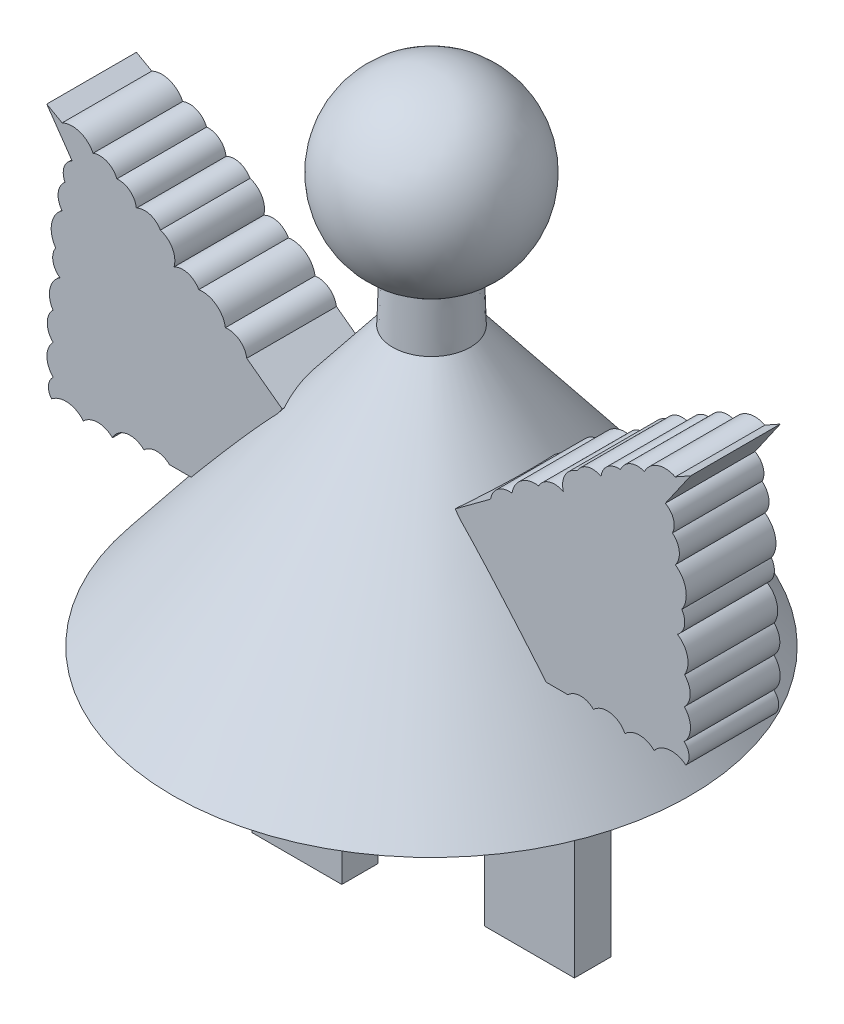
SolidWorks part; units mm, degrees
ref_plane "Front Plane" through (0, 0, 0) normal (0, 0, 1) x (1, 0, 0)
ref_plane "Top Plane" through (0, 0, 0) normal (0, 1, 0) x (1, 0, 0)
ref_plane "Right Plane" through (0, 0, 0) normal (1, 0, 0) x (0, 0, -1)
sketch "Sketch1" plane through (0, 0, 0) normal (0, 0, 1) x (1, 0, 0)
  line L0 (0, 0) -> (0, -70.8128) construction
  line L1 (5.4979, -31.3897) -> (5.2821, -24.2494)
  line L2 (5.4979, -31.3897) -> (36.6314, -70.8128)
  line L3 (36.6314, -70.8128) -> (0, -70.8128)
  line L4 (0, 0) -> (0, -70.8128)
  arc A0 (0, 0) -> (5.2821, -24.2494) centre (0, -12.7) cw
  dimension "D1" = 12.7
revolve "Revolve1" add sketch "Sketch1" angle 360 about L0
sketch "Sketch2" plane through (0, -70.8128, 0) normal (0, -1, 0) x (-1, 0, 0)
  line L1 (20.32, -5.08) -> (7.62, -5.08)
  line L2 (20.32, -5.08) -> (20.32, 0.0781)
  line L3 (20.32, 0.0781) -> (7.62, 0.0781)
  line L4 (7.62, -5.08) -> (7.62, 0.0781)
  line L5 (-7.62, -0.0781) -> (-20.32, -0.0781)
  line L6 (-7.62, -0.0781) -> (-7.62, 5.08)
  line L7 (-7.62, 5.08) -> (-20.32, 5.08)
  line L8 (-20.32, -0.0781) -> (-20.32, 5.08)
  circle A0 centre (0, 0) radius 36.6314 construction
  dimension "D8" = 5.08
  dimension "D1" = 12.7
  dimension "D2" = 12.7
  dimension "D3" = 7.62
  dimension "D4" = 7.62
  dimension "D5" = 5.1581
  dimension "D6" = 5.1581
  dimension "D7" = 5.08
extrude "Boss-Extrude1" add sketch "Sketch2" along normal blind 30.48
ref_plane "Plane4" through (0, 0, 2.54) normal (0, 0, 1) x (1, 0, 0)
sketch "Sketch4" plane through (0, 0, 2.54) normal (0, 0, 1) x (1, 0, 0)
  line L0 (23.1944, -58.1954) -> (28.2187, -58.1954)
  line L3 (12.2505, -43.3865) -> (17.2708, -39.6764)
  line L4 (43.4204, -23.8719) -> (45.598, -22.6536)
  line L6 (45.598, -22.6536) -> (42.0022, -27.8276)
  line L7 (0, 0) -> (0, -69.3999) construction
  line L8 (12.2505, -43.3865) -> (23.1944, -58.1954)
  line L9 (-23.1944, -58.1954) -> (-28.2187, -58.1954)
  line L10 (-45.598, -22.6536) -> (-42.0022, -27.8276)
  line L11 (-43.4204, -23.8719) -> (-45.598, -22.6536)
  line L12 (-12.2505, -43.3865) -> (-17.2708, -39.6764)
  line L13 (-12.2505, -43.3865) -> (-23.1944, -58.1954)
  arc A0 (28.2187, -58.1954) -> (31.8362, -58.1954) centre (30.0274, -60.0042) cw
  arc A1 (36.286, -58.9371) -> (40.41, -58.9371) centre (38.348, -60.999) cw
  arc A2 (31.8362, -58.1954) -> (36.286, -58.9371) centre (33.7963, -60.1555) cw
  arc A3 (40.41, -58.9371) -> (44.9103, -58.4745) centre (42.8914, -60.956) cw
  arc A4 (17.2708, -39.6764) -> (20.2997, -37.4381) centre (19.9044, -40.0717) cw
  arc A5 (20.2997, -37.4381) -> (24.0687, -34.6528) centre (23.5768, -37.93) cw
  arc A6 (24.0687, -34.6528) -> (27.5739, -33.6239) centre (26.3357, -35.891) cw
  arc A7 (27.5739, -33.6239) -> (29.5116, -30.0761) centre (30.3167, -32.8188) cw
  arc A8 (29.5116, -30.0761) -> (32.9082, -29.0791) centre (31.7084, -31.2758) cw
  arc A9 (32.9082, -29.0791) -> (35.6613, -26.8608) centre (35.3939, -29.3465) cw
  arc A10 (35.6613, -26.8608) -> (39.0437, -25.4121) centre (38.0769, -27.8276) cw
  arc A11 (39.0437, -25.4121) -> (43.4204, -23.8719) centre (42.0022, -26.8303) cw
  arc A12 (43.4204, -34.6528) -> (44.3312, -39.6764) centre (41.364, -37.62) cw
  arc A13 (44.3312, -39.6764) -> (43.7236, -43.0242) centre (42.3535, -41.0466) cw
  arc A14 (43.7236, -43.0242) -> (44.7208, -47.4885) centre (41.9901, -45.7549) cw
  arc A15 (44.7208, -47.4885) -> (44.6981, -51.4349) centre (42.7362, -49.4504) cw
  arc A16 (44.6981, -51.4349) -> (44.6732, -55.723) centre (42.5416, -53.5665) cw
  arc A17 (44.6732, -55.723) -> (44.9103, -58.4745) centre (43.416, -57.2173) cw
  arc A18 (42.0022, -27.8276) -> (43.0117, -30.9593) centre (40.9411, -29.8982) cw
  arc A19 (43.0117, -30.9593) -> (43.4204, -34.6528) centre (41.3693, -33.0104) cw
  arc A20 (-28.2187, -58.1954) -> (-31.8362, -58.1954) centre (-30.0274, -60.0042) ccw
  arc A21 (-31.8362, -58.1954) -> (-36.286, -58.9371) centre (-33.7963, -60.1555) ccw
  arc A22 (-36.286, -58.9371) -> (-40.41, -58.9371) centre (-38.348, -60.999) ccw
  arc A23 (-40.41, -58.9371) -> (-44.9103, -58.4745) centre (-42.8914, -60.956) ccw
  arc A24 (-44.6732, -55.723) -> (-44.9103, -58.4745) centre (-43.416, -57.2173) ccw
  arc A25 (-44.6981, -51.4349) -> (-44.6732, -55.723) centre (-42.5416, -53.5665) ccw
  arc A26 (-44.7208, -47.4885) -> (-44.6981, -51.4349) centre (-42.7362, -49.4504) ccw
  arc A27 (-43.7236, -43.0242) -> (-44.7208, -47.4885) centre (-41.9901, -45.7549) ccw
  arc A28 (-44.3312, -39.6764) -> (-43.7236, -43.0242) centre (-42.3535, -41.0466) ccw
  arc A29 (-43.4204, -34.6528) -> (-44.3312, -39.6764) centre (-41.364, -37.62) ccw
  arc A30 (-43.0117, -30.9593) -> (-43.4204, -34.6528) centre (-41.3693, -33.0104) ccw
  arc A31 (-42.0022, -27.8276) -> (-43.0117, -30.9593) centre (-40.9411, -29.8982) ccw
  arc A32 (-32.9082, -29.0791) -> (-35.6613, -26.8608) centre (-35.3939, -29.3465) ccw
  arc A33 (-39.0437, -25.4121) -> (-43.4204, -23.8719) centre (-42.0022, -26.8303) ccw
  arc A34 (-35.6613, -26.8608) -> (-39.0437, -25.4121) centre (-38.0769, -27.8276) ccw
  arc A35 (-29.5116, -30.0761) -> (-32.9082, -29.0791) centre (-31.7084, -31.2758) ccw
  arc A36 (-27.5739, -33.6239) -> (-29.5116, -30.0761) centre (-30.3167, -32.8188) ccw
  arc A37 (-24.0687, -34.6528) -> (-27.5739, -33.6239) centre (-26.3357, -35.891) ccw
  arc A38 (-20.2997, -37.4381) -> (-24.0687, -34.6528) centre (-23.5768, -37.93) ccw
  arc A39 (-17.2708, -39.6764) -> (-20.2997, -37.4381) centre (-19.9044, -40.0717) ccw
extrude "Boss-Extrude2" add sketch "Sketch4" along normal mid plane 12.7
sketch "Sketch5" plane through (0, 0, 2.54) normal (0, 0, 1) x (1, 0, 0)
  line L0 (0, -71.1765) -> (0, 0) construction
